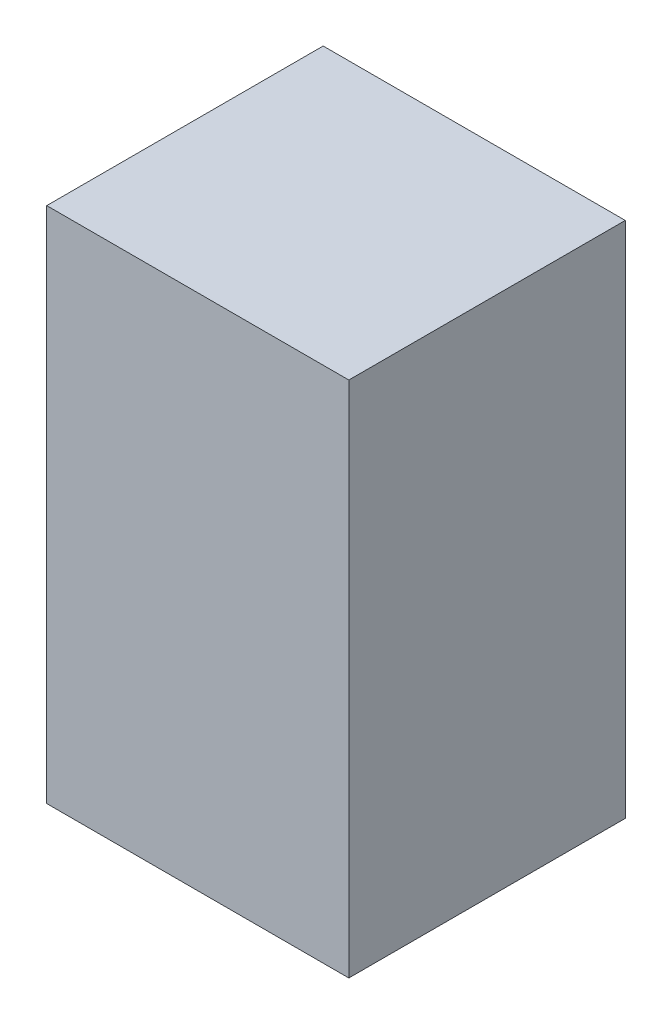
SolidWorks part; units mm, degrees
ref_plane "Front Plane" through (0, 0, 0) normal (0, 0, 1) x (1, 0, 0)
ref_plane "Top Plane" through (0, 0, 0) normal (0, 1, 0) x (1, 0, 0)
ref_plane "Right Plane" through (0, 0, 0) normal (1, 0, 0) x (0, 0, -1)
sketch "Sketch1" plane through (0, 0, 0) normal (0, 0, 1) x (1, 0, 0)
  line L1 (-3.6509, 15.2882) -> (22.2491, 15.2882)
  line L2 (-3.6509, 15.2882) -> (-3.6509, -29.1118)
  line L3 (-3.6509, -29.1118) -> (22.2491, -29.1118)
  line L4 (22.2491, 15.2882) -> (22.2491, -29.1118)
  dimension "D1" = 25.9
  dimension "D2" = 44.4
extrude "Boss-Extrude1" add sketch "Sketch1" along normal blind 23.7
